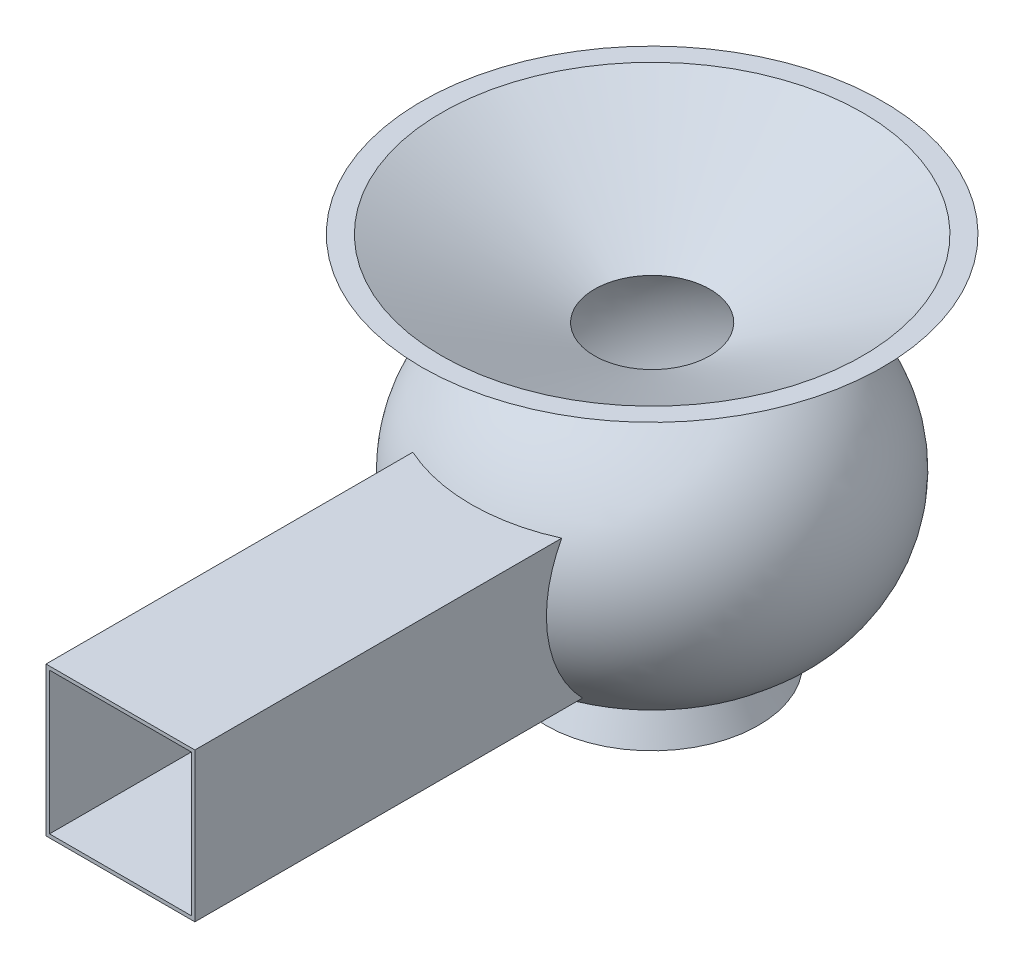
SolidWorks part; units mm, degrees
ref_plane "Front Plane" through (0, 0, 0) normal (0, 0, 1) x (1, 0, 0)
ref_plane "Top Plane" through (0, 0, 0) normal (0, 1, 0) x (1, 0, 0)
ref_plane "Right Plane" through (0, 0, 0) normal (1, 0, 0) x (0, 0, -1)
sketch "Sketch1" plane through (0, 0, 0) normal (0, 0, 1) x (1, 0, 0)
  line L2 (42.5378, 23.744) -> (51.9098, 5)
  line L3 (130, 210) -> (50, 170)
  line L4 (0, 0) -> (60, 0)
  line L6 (50, 20) -> (60, 0)
  line L10 (5, 5) -> (5, 205) construction
  line L11 (5, 5) -> (51.9098, 5) construction
  line L12 (51.9098, 5) -> (0, 5)
  line L14 (5, 205) -> (108.8197, 205) construction
  line L15 (0, 5) -> (0, 0)
  line L16 (0, 0) -> (0, 210) construction
  line L18 (0, 220.652) -> (0, 5)
  line L19 (32.5653, 166.8728) -> (118.8197, 210)
  line L20 (108.8197, 205) -> (32.5653, 166.8728) construction
  line L21 (130, 210) -> (118.8197, 210)
  line L22 (0, 210) -> (130, 210) construction
  arc A0 (50, 170) -> (50, 20) centre (33.125, 95) cw
  arc A1 (32.5653, 166.8728) -> (42.5378, 23.744) centre (33.125, 95) cw
  dimension "D2" = 5
  dimension "D5" = 60
revolve "Revolve3" add sketch "Sketch1" angle 360 about L18
ref_plane "Plane1" through (0, 0, 300) normal (0, 0, 1) x (1, 0, 0)
sketch "Sketch2" plane through (0, 0, 300) normal (0, 0, 1) x (1, 0, 0)
  line L0 (-42, 45) -> (38, 45) construction
  line L1 (-42, 129) -> (42, 129)
  line L2 (-42, 129) -> (-42, 45)
  line L3 (-42, 45) -> (42, 45)
  line L4 (42, 129) -> (42, 45)
  line L5 (-36.3, 47.9) -> (37.2, 47.9) construction
  dimension "D1" = 0
  dimension "84" = 84
  dimension "D2" = 84
  dimension "D3" = 42
  dimension "D4" = 2.9
extrude "Boss-Extrude1" add sketch "Sketch2" against normal up to surface (206.9688 mm away)
sketch "Sketch4" plane through (0, 0, 300) normal (0, 0, 1) x (1, 0, 0)
  line L0 (-42, 129) -> (-42, 45) construction
  line L1 (-40, 127) -> (40, 127)
  line L2 (-40, 127) -> (-40, 47)
  line L3 (-40, 47) -> (40, 47)
  line L4 (40, 127) -> (40, 47)
  line L5 (42, 129) -> (-42, 129) construction
  dimension "D1" = 80
  dimension "D2" = 2
  dimension "D3" = 80
  dimension "D4" = 2
extrude "Cut-Extrude2" cut sketch "Sketch4" against normal up to next
